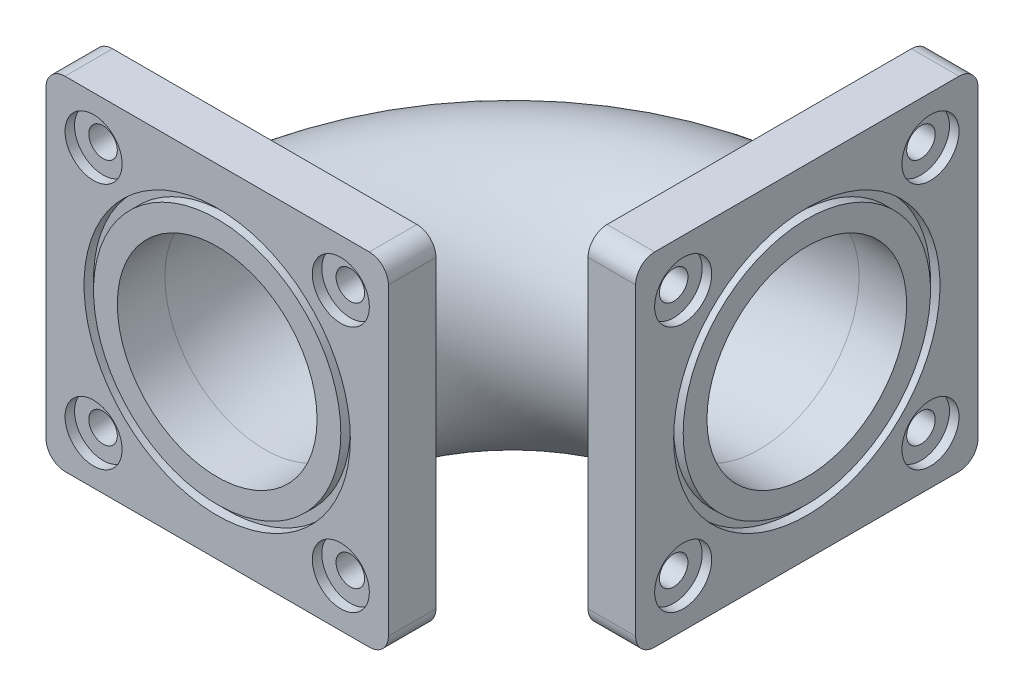
SolidWorks part; units mm, degrees
material "AISI 1020"
ref_plane "Front Plane" through (0, 0, 0) normal (0, 0, 1) x (1, 0, 0)
ref_plane "Top Plane" through (0, 0, 0) normal (0, 1, 0) x (1, 0, 0)
ref_plane "Right Plane" through (0, 0, 0) normal (1, 0, 0) x (0, 0, -1)
sketch "Sketch3" plane through (0, 0, 0) normal (0, 0, 1) x (1, 0, 0)
  line L0 (0, 20.5369) -> (0, -20.0167) construction
  circle A0 centre (-26, 0) radius 10.5
  circle A1 centre (-26, 0) radius 13
  dimension "D1" = 21
  dimension "D2" = 26
  dimension "D3" = 26
revolve "Revolve2" add sketch "Sketch3" angle 90 about L0
sketch "Sketch5" plane through (0, 0, 0) normal (0, 0, 1) x (1, 0, 0)
  line L1 (-44, -18) -> (-8, -18)
  line L2 (-44, -18) -> (-44, 18)
  line L3 (-44, 18) -> (-8, 18)
  line L4 (-8, -18) -> (-8, 18)
  line L5 (-44, -18) -> (-8, 18) construction
  line L6 (-44, 18) -> (-8, -18) construction
  circle A0 centre (-26, 0) radius 10.5 construction
  circle A3 centre (-26, 0) radius 10.5
  point P0 (-26, 0)
  dimension "D1" = 36
extrude "Boss-Extrude3" add sketch "Sketch5" along normal blind 5
sketch "Sketch6" plane through (0, 0, 5) normal (0, 0, 1) x (1, 0, 0)
  circle A0 centre (-26, 0) radius 13
  circle A1 centre (-26, 0) radius 14
  circle A2 centre (-26, 0) radius 10.5 construction
  circle A3 centre (-26, 0) radius 10.5
  dimension "D1" = 26
  dimension "D2" = 28
extrude "Cut-Extrude1" cut sketch "Sketch6" against normal blind 1 contours A1 A0
fillet "Fillet1" radius 2 4 edges at (-8, 18, 2.5) (-8, -18, 2.5) (-44, -18, 2.5) (-44, 18, 2.5)
fillet "Fillet2" radius 2 1 edges at (-13, 0, 0)
hole_wizard "CBORE for M5 Hex Head Bolt1" positions "Sketch7" profile "Sketch8" counterbore size "M5" standard "ANSI Metric"
sketch "Sketch7" plane through (0, 0, 5) normal (0, 0, 1) x (1, 0, 0)
  line L0 (-44, 0) -> (-8, 0) construction
  line L1 (-44, 16) -> (-44, -16) construction
  line L2 (-8, -16) -> (-8, 16) construction
  line L3 (-26, -18) -> (-26, 18) construction
  line L4 (-42, -18) -> (-10, -18) construction
  line L5 (-10, 18) -> (-42, 18) construction
  point P0 (-39, -13)
  point P16 (-39, 13)
  point P17 (-13, 13)
  point P18 (-13, -13)
  dimension "D1" = 5
  dimension "D2" = 5
sketch "Sketch8" plane through (-39, -13, 5) normal (1, 0, 0) x (0, -1, 0)
  line L0 (0, 0) -> (0, 11)
  line L1 (0, 11) -> (1.5, 10.0987)
  line L2 (1.5, 10.0987) -> (1.5, 1)
  line L3 (1.5, 1) -> (3, 1)
  line L4 (3, 1) -> (3, 0)
  line L5 (3, 0) -> (0, 0)
  line L10 (0, 11) -> (-1.5, 10.0987) construction
  line L11 (0, -6.35) -> (0, 107.95) construction
  dimension "Hole Dia." = 3
  dimension "Hole Depth" = 11
  dimension "C'Bore Dia." = 6
  dimension "C'Bore Depth" = 1
  dimension "Drill Angle" = 118
sketch "Sketch9" plane through (0, -18, 0) normal (0, -1, 0) x (1, 0, 0)
  line L0 (0, 0) -> (0, -26) construction
  line L1 (0, 0) -> (-26, 0) construction
  line L2 (0, 0) -> (-38.4866, -38.4866) construction
  circle A0 centre (0, 0) radius 26
  dimension "D1" = 52
  dimension "D2" = 45
sketch "Sketch10" plane through (0, 0, 0) normal (1, 0, 0) x (0, 0, -1)
  line L0 (0, -18) -> (0, 35.4351) construction
ref_plane "Plane1" through (0, 0, 0) normal (-0.7071, 0, 0.7071) x (0.7071, 0, 0.7071)
mirror "Mirror1" about plane through (0, 0, 0) normal (-0.7071, 0, 0.7071) of "CBORE for M5 Hex Head Bolt1", "Fillet1", "Cut-Extrude1", "Boss-Extrude3", "Fillet2"
sketch "Sketch11" plane through (0, 0, 5) normal (0, 0, 1) x (1, 0, 0)
  line L0 (-39.5575, 18) -> (-44, 18) construction
  line L1 (-10, 18) -> (-42, 18) construction
  line L2 (-44, 13.3587) -> (-44, 18) construction
  line L3 (-44, 16) -> (-44, -16) construction
